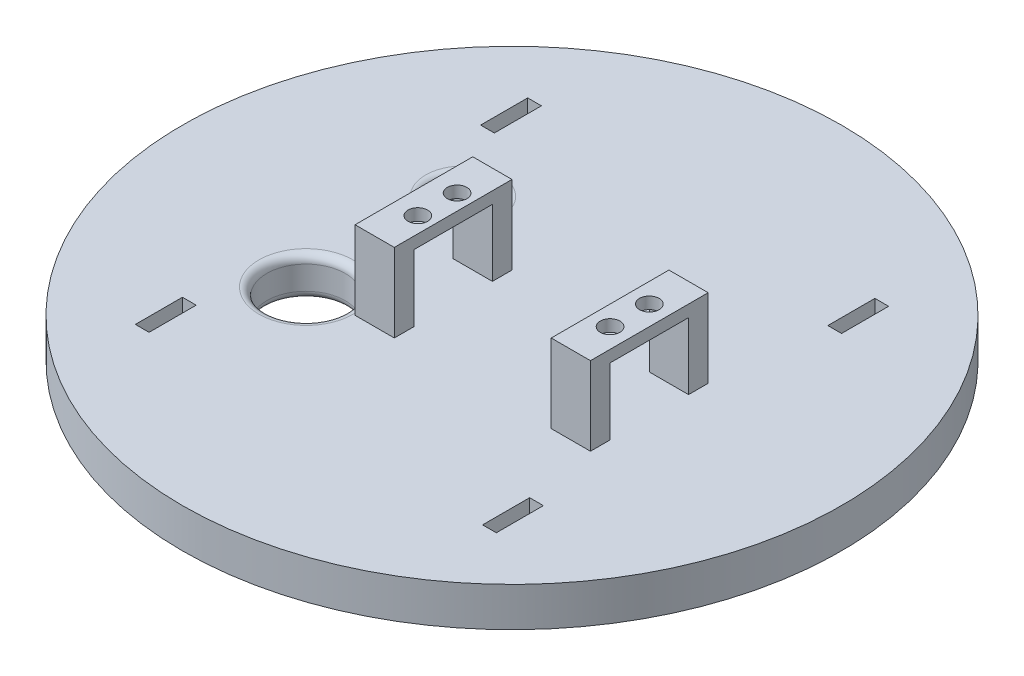
SolidWorks part; units mm, degrees
ref_plane "Front Plane" through (0, 0, 0) normal (0, 0, 1) x (1, 0, 0)
ref_plane "Top Plane" through (0, 0, 0) normal (0, 1, 0) x (1, 0, 0)
ref_plane "Right Plane" through (0, 0, 0) normal (1, 0, 0) x (0, 0, -1)
sketch "Sketch1" plane through (0, 0, 0) normal (0, 1, 0) x (1, 0, 0)
  circle A0 centre (0, 0) radius 84
extrude "base" add sketch "Sketch1" along normal blind 10 contours A0
sketch "Sketch3" plane through (0, 10, 0) normal (0, 1, 0) x (1, 0, 0)
  line L0 (-20, 10) -> (-10, 10)
  line L1 (-20, 10) -> (-20, -20)
  line L2 (-20, -20) -> (-10, -20)
  line L3 (-10, 10) -> (-10, -20)
  line L4 (30, 10) -> (40, 10)
  line L5 (30, 10) -> (30, -20)
  line L6 (30, -20) -> (40, -20)
  line L7 (40, 10) -> (40, -20)
  line L8 (-20, 5) -> (-10, 5)
  line L9 (-10, -15) -> (-20, -15)
  line L10 (30, 5) -> (40, 5)
  line L11 (30, -15) -> (40, -15)
  dimension "D1" = 30
  dimension "D2" = 10
  dimension "D3" = 30
  dimension "D4" = 10
  dimension "D5" = 10
  dimension "D7" = 10
  dimension "D8" = 30
  dimension "D9" = 5
  dimension "D10" = 5
  dimension "D11" = 5
  dimension "D12" = 5
extrude "motor mounts (both)" add sketch "Sketch3" along normal blind 20 contours L1 L8 L3 L0 | L3 L9 L1 L2 | L11 L5 L6 L7 | L5 L10 L7 L4
sketch "Sketch4" plane through (0, 30, 0) normal (0, 1, 0) x (1, 0, 0)
  line L0 (-10, 5) -> (-10, -15)
  line L1 (-10, -15) -> (-20, -15)
  line L2 (-20, -15) -> (-20, 5)
  line L3 (-20, 5) -> (-10, 5)
  line L4 (30, 5) -> (40, 5)
  line L5 (40, 5) -> (40, -15)
  line L6 (40, -15) -> (30, -15)
  line L7 (30, -15) -> (30, 5)
  circle A0 centre (-14, 0) radius 2.5
  circle A1 centre (-14, -10) radius 2.5
  circle A2 centre (35, 0) radius 2.5
  circle A3 centre (35, -10) radius 2.5
  dimension "D2" = 5
  dimension "D4" = 5
  dimension "D8" = 5
  dimension "D9" = 5
  dimension "D1" = 5
  dimension "D3" = 10
  dimension "D5" = 14
  dimension "D6" = 5
  dimension "D7" = 10
  dimension "D10" = 35
extrude "motor screw holes" add sketch "Sketch4" against normal blind 3
sketch "Sketch5" plane through (0, 0, 0) normal (0, -1, 0) x (1, 0, 0)
  circle A0 centre (0, 0) radius 10.3
  dimension "D1" = 20.6
extrude "gear hole" cut sketch "Sketch5" against normal blind 5.1 contours A0
sketch "Sketch6" plane through (0, 10, 0) normal (0, 1, 0) x (1, 0, 0)
  circle A0 centre (-32.5, 20) radius 7.5
  circle A2 centre (-32.5, -20) radius 10
  dimension "D3" = 15
  dimension "D5" = 20
  dimension "D6" = 20
  dimension "D1" = 32.5
  dimension "D2" = 20
  dimension "D4" = 32.5
extrude "wire holes" cut sketch "Sketch6" against normal up to next
sketch "Sketch7" plane through (0, 10, 0) normal (0, 1, 0) x (1, 0, 0)
  line L0 (-42.5, 47.5) -> (-42.5, 50)
  line L1 (-46, 50) -> (46, 50)
  line L2 (-46, 50) -> (-46, -50)
  line L3 (-46, -50) -> (46, -50)
  line L4 (46, 50) -> (46, -50)
  line L5 (-42.5, 47.5) -> (42.5, 47.5)
  line L6 (-42.5, 47.5) -> (-42.5, -47.5)
  line L7 (-42.5, -47.5) -> (42.5, -47.5)
  line L8 (42.5, 47.5) -> (42.5, -47.5)
  line L9 (-42.5, 38) -> (-46, 38)
  line L10 (-46, -38) -> (-42.5, -38)
  line L11 (-42.5, -47.5) -> (-42.5, -50)
  line L12 (42.5, 47.5) -> (42.5, 50)
  line L13 (42.5, 38) -> (46, 38)
  line L14 (42.5, -47.5) -> (42.5, -50)
  line L15 (42.5, -38) -> (46, -38)
  dimension "D1" = 50
  dimension "D2" = 100
  dimension "D3" = 92
  dimension "D4" = 46
  dimension "D5" = 95
  dimension "D6" = 85
  dimension "D7" = 2.5
  dimension "D8" = 3.5
  dimension "D9" = 12
  dimension "D10" = 3.5
  dimension "D11" = 12
  dimension "D12" = 12
  dimension "D13" = 12
  dimension "D14" = 12
  dimension "D15" = 12
  dimension "D16" = 3.5
  dimension "D17" = 3.5
  dimension "D18" = 3.5
  dimension "D19" = 12
extrude "Cut-Extrude1" cut sketch "Sketch7" against normal up to next contours L9 L6 L0 L1 L2 | L8 L13 L4 L1 L12 | L15 L8 L14 L3 L4 | L11 L6 L10 L2 L3
fillet "Fillet2" radius 2 4 edges at (-32.5, 10, -12.5) (-32.5, 10, 30) (-32.5, 0, -12.5) (-32.5, 0, 30)
